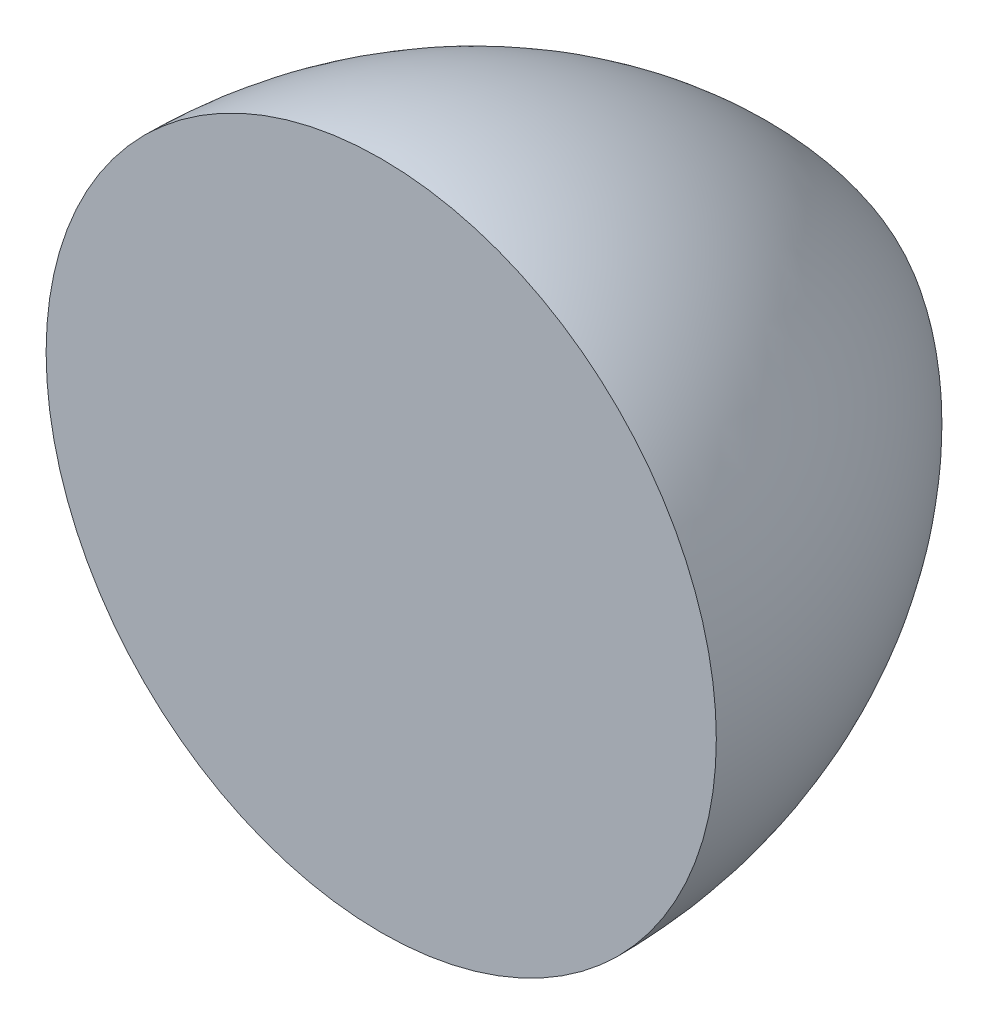
SolidWorks part; units mm, degrees
material "PVC 0.007 Plasticized"
ref_plane "Front Plane" through (0, 0, 0) normal (0, 0, 1) x (1, 0, 0)
ref_plane "Top Plane" through (0, 0, 0) normal (0, 1, 0) x (1, 0, 0)
ref_plane "Right Plane" through (0, 0, 0) normal (1, 0, 0) x (0, 0, -1)
sketch "Sketch1" plane through (0, 0, 0) normal (1, 0, 0) x (0, 0, -1)
  line L0 (0, 0) -> (0, 100)
  line L1 (0, 0) -> (150, 0)
  line L2 (0, 0) -> (150, 0) construction
  arc A1 (0, 100) -> (150, 0) centre (0, -62.5) cw
  dimension "D1" = 100
  dimension "D2" = 150
revolve "Revolve2" add sketch "Sketch1" angle 360 about L2
